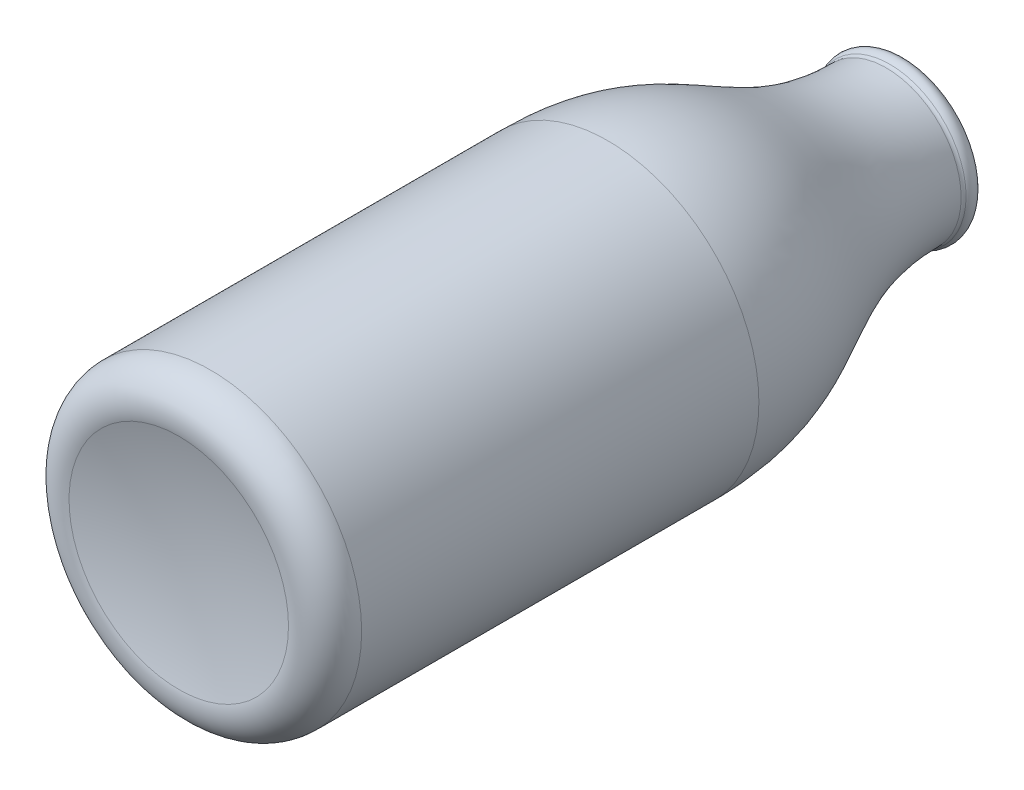
SolidWorks part; units mm, degrees
ref_plane "Ebene vorne" through (0, 0, 0) normal (0, 0, 1) x (1, 0, 0)
ref_plane "Ebene oben" through (0, 0, 0) normal (0, 1, 0) x (1, 0, 0)
ref_plane "Ebene rechts" through (0, 0, 0) normal (1, 0, 0) x (0, 0, -1)
sketch "Skizze1" plane through (0, 0, 0) normal (1, 0, 0) x (0, 0, -1)
  line L0 (0, 0) -> (130.1846, 0) construction
  line L1 (6.4331, 26.5021) -> (78.7753, 26.5021)
  line L2 (130.1846, 12.6358) -> (154.4877, 12.6358) construction
  line L3 (129.4721, 12.64) -> (132.2469, 12.6365)
  line L4 (6.4331, 27.5021) -> (78.7753, 27.5021)
  line L7 (3.199, 0) -> (4.199, 0)
  line L8 (132.862, 12.6358) -> (132.862, 11.838) construction
  line L9 (131.862, 12.6358) -> (131.862, 11.838) construction
  arc A0 (4.199, 0) -> (1.5959, 20.2367) centre (-75.764, 0) ccw
  arc A1 (6.4331, 26.5021) -> (1.5959, 20.2367) centre (6.4331, 21.5021) ccw
  arc A3 (132.862, 12.6358) -> (130.1272, 13.8844) centre (131.2095, 12.6358) ccw construction
  arc A4 (3.199, 0) -> (0.6284, 19.9836) centre (-75.764, 0) ccw
  arc A5 (6.4331, 27.5021) -> (0.6284, 19.9836) centre (6.4331, 21.5021) ccw
  arc A6 (129.4721, 13.64) -> (130.1272, 13.8844) centre (129.4721, 14.64) ccw
  arc A7 (132.6978, 13.3538) -> (130.1272, 13.8844) centre (131.2095, 12.6358) ccw
  arc A9 (132.6978, 13.3538) -> (132.2469, 12.6365) centre (132.2475, 13.1365) cw
  arc A11 (131.862, 12.6358) -> (130.7822, 13.1288) centre (131.2095, 12.6358) ccw construction
  arc A12 (129.4721, 12.64) -> (130.7822, 13.1288) centre (129.4721, 14.64) ccw construction
  spline S0 degree 3 poles (78.7753, 26.5021) (85.7681, 26.5021) (97.2236, 24.437) (112.7617, 14.6898) (123.5615, 12.64) (129.4721, 12.64) knots 0 0 0 0 0.3567 0.679311 0.987665 0.987665 0.987665 0.987665
  spline S1 degree 1 poles (78.7753, 27.5021) (129.4721, 13.64) knots 0 0 1 1 construction
  spline S2 degree 3 poles (78.7753, 27.5021) (79.3825, 27.5021) (80.6064, 27.4856) (82.9771, 27.3855) (85.8576, 27.1325) (89.1875, 26.6164) (93.4906, 25.6397) (98.6808, 23.8392) (104.6875, 20.8283) (110.5967, 17.7453) (115.5358, 15.7506) (119.6219, 14.66) (122.7753, 14.0716) (125.5001, 13.7776) (127.7415, 13.6596) (128.8982, 13.64) (129.4721, 13.64) knots 0 0 0 0 0.030865 0.061729 0.123458 0.185187 0.246916 0.370374 0.493832 0.61729 0.740748 0.802478 0.864207 0.925936 0.9568 0.987665 0.987665 0.987665 0.987665
revolve "Rotation1" add sketch "Skizze1" angle 360 about L0
